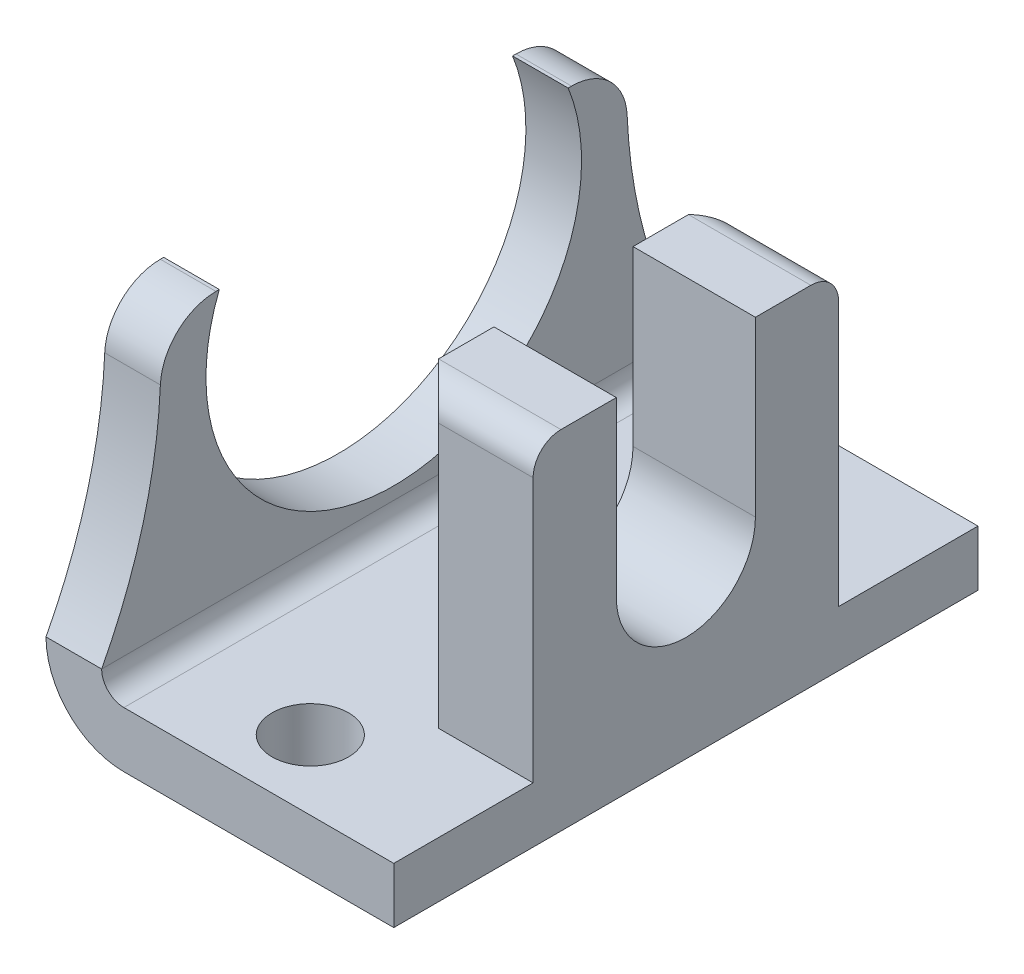
SolidWorks part; units mm, degrees
ref_plane "Ebene vorne" through (0, 0, 0) normal (0, 0, 1) x (1, 0, 0)
ref_plane "Ebene oben" through (0, 0, 0) normal (0, 1, 0) x (1, 0, 0)
ref_plane "Ebene rechts" through (0, 0, 0) normal (1, 0, 0) x (0, 0, -1)
ref_plane "Ebene1" through (25, 0, 0) normal (1, 0, 0) x (0, 0, -1)
sketch "Skizze1" plane through (25, 0, 0) normal (1, 0, 0) x (0, 0, -1)
  line L0 (21, 0) -> (21, 25)
  line L1 (21, 25) -> (-21, 25)
  line L2 (-21, 25) -> (-21, 0)
  line L3 (-21, 0) -> (21, 0)
extrude "Aufsatz-Linear austragen1" add sketch "Skizze1" against normal blind 25
sketch "Skizze2" plane through (0, 0, 21) normal (0, 0, 1) x (1, 0, 0)
  line L0 (4, 4) -> (25, 4)
  line L1 (25, 4) -> (25, 25)
  line L2 (25, 25) -> (4, 25)
  line L3 (4, 25) -> (4, 4)
extrude "Schnitt-Linear austragen1" cut sketch "Skizze2" against normal through all
sketch "Skizze3" plane through (4, 0, 0) normal (1, 0, 0) x (0, 0, -1)
  line L0 (-21, 25) -> (-21, 5.6)
  line L1 (-16.8076, 25) -> (-21, 25)
  arc A0 (-21, 5.6) -> (-16.8076, 25) centre (-53.6093, 22.8) ccw
extrude "Schnitt-Linear austragen2" cut sketch "Skizze3" against normal through all
sketch "Skizze4" plane through (0, 4, 0) normal (0, 1, 0) x (-1, 0, 0)
  line L0 (-25, -10.982) -> (-25, 10.982)
  line L1 (-25, 10.982) -> (-16.2, 10.982)
  line L2 (-16.2, 10.982) -> (-16.2, -10.982)
  line L3 (-16.2, -10.982) -> (-25, -10.982)
extrude "Aufsatz-Linear austragen2" add sketch "Skizze4" along normal blind 21
sketch "Skizze5" plane through (25, 0, 0) normal (1, 0, 0) x (0, 0, -1)
  line L0 (5, 25) -> (-5, 25)
  line L1 (-5, 25) -> (-5, 12.5604)
  line L2 (5, 12.5604) -> (5, 25)
  arc A0 (-5, 12.5604) -> (5, 12.5604) centre (0, 12.5604) ccw
extrude "Schnitt-Linear austragen3" cut sketch "Skizze5" against normal up to next
sketch "Skizze6" plane through (4, 0, 0) normal (1, 0, 0) x (0, 0, -1)
  line L0 (21, 25) -> (16.8076, 25)
  line L1 (21, 5.6) -> (21, 25)
  arc A0 (16.8076, 25) -> (21, 5.6) centre (53.6093, 22.8) ccw
extrude "Schnitt-Linear austragen4" cut sketch "Skizze6" against normal through all
hole_wizard "Durchgangsloch für M241" positions "Skizze8" profile "Skizze7" hole size "M24" standard "ANSI Metric"
sketch "Skizze8" plane through (4, 0, 0) normal (1, 0, 0) x (0, 0, -1)
  point P0 (0, 20)
sketch "Skizze7" plane through (4, 20, 0) normal (0, 1, 0) x (0, 0, -1)
  line L0 (0, 0) -> (0, 4)
  line L1 (0, 4) -> (13.5, 4)
  line L2 (13.5, 4) -> (13.5, 0)
  line L5 (13.5, 0) -> (0, 0)
  line L11 (0, -6.35) -> (0, 107.95) construction
  dimension "Bohrerdurchmesser" = 27
  dimension "Bohrungstiefe" = 4
hole_wizard "Ø5.5 (5.5) Durchmesser Bohrung1" positions "Skizze10" profile "Skizze9" hole size "Ø5.5" standard "ANSI Metric"
sketch "Skizze10" plane through (0, 0, 0) normal (0, -1, 0) x (-1, 0, 0)
  point P0 (-14, -16)
  point P1 (-14, 16)
sketch "Skizze9" plane through (14, 0, 16) normal (1, 0, 0) x (0, 0, -1)
  line L0 (0, 0) -> (0, 25)
  line L1 (0, 25) -> (2.75, 25)
  line L2 (2.75, 25) -> (2.75, 0)
  line L5 (2.75, 0) -> (0, 0)
  line L11 (0, -6.35) -> (0, 107.95) construction
  dimension "Bohrerdurchmesser" = 5.5
  dimension "Bohrungstiefe" = 25
chamfer "Fase1" distance 2 angle 45 2 edges at (16.2, 14.5, -10.982) (16.2, 14.5, 10.982)
fillet "Verrundung1" radius 1.6 1 edges at (4, 4, 0)
fillet "Verrundung2" radius 2 2 edges at (21.6, 25, 10.982) (21.6, 25, -10.982)
fillet "Verrundung3" radius 4 2 edges at (2, 25, -16.8076) (2, 25, 16.8076)
fillet "Verrundung4" radius 5.6 1 edges at (0, 0, 0)
